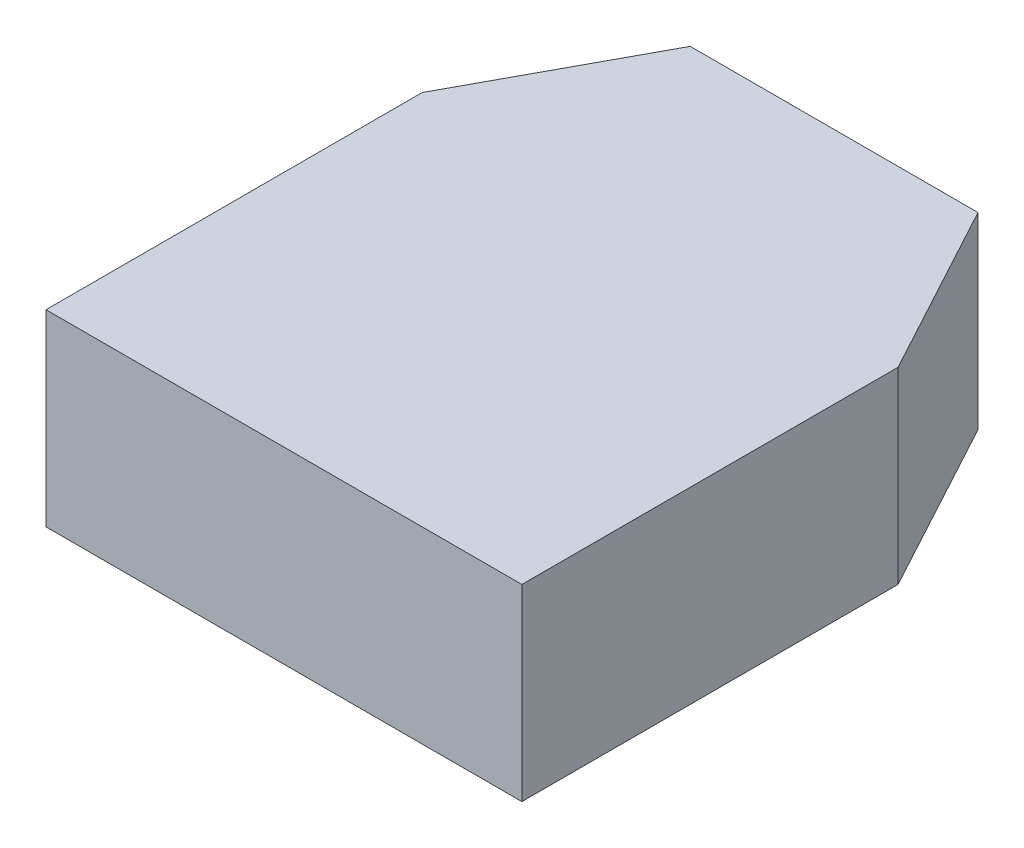
SolidWorks part; units mm, degrees
ref_plane "Front Plane" through (0, 0, 0) normal (0, 0, 1) x (1, 0, 0)
ref_plane "Top Plane" through (0, 0, 0) normal (0, 1, 0) x (1, 0, 0)
ref_plane "Right Plane" through (0, 0, 0) normal (1, 0, 0) x (0, 0, -1)
sketch "Sketch1" plane through (0, 0, 0) normal (0, 1, 0) x (1, 0, 0)
  line L0 (-50.6, 40) -> (-40.6, 58.5)
  line L1 (-40.6, 58.5) -> (-10, 58.5)
  line L2 (-10, 58.5) -> (0, 40)
  line L3 (0, 40) -> (0, 0)
  line L4 (0, 0) -> (-50.6, 0)
  line L5 (-50.6, 0) -> (-50.6, 40)
  dimension "D1" = 50.6
  dimension "D2" = 40
  dimension "D3" = 10
  dimension "D4" = 30.6
  dimension "D5" = 18.5
extrude "Boss-Extrude1" add sketch "Sketch1" along normal blind 20
